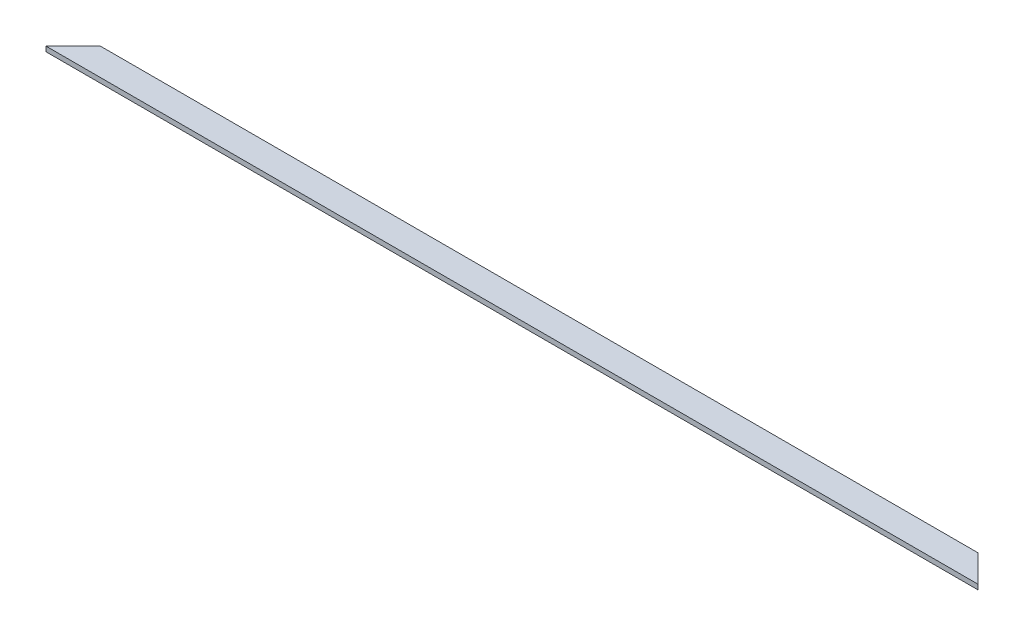
SolidWorks part; units mm, degrees
ref_plane "Front Plane" through (0, 0, 0) normal (0, 0, 1) x (1, 0, 0)
ref_plane "Top Plane" through (0, 0, 0) normal (0, 1, 0) x (1, 0, 0)
ref_plane "Right Plane" through (0, 0, 0) normal (1, 0, 0) x (0, 0, -1)
sketch "Sketch1" plane through (0, 0, 0) normal (0, 1, 0) x (1, 0, 0)
  line L0 (4787.9, 0) -> (4648.2, 139.7)
  line L1 (0, 0) -> (4787.9, 0)
  line L3 (139.7, 139.7) -> (4648.2, 139.7)
  line L4 (0, 0) -> (139.7, 139.7)
  dimension "D1" = 45
  dimension "D2" = 4787.9
  dimension "D3" = 139.7
  dimension "D4" = 45
extrude "Boss-Extrude1" add sketch "Sketch1" along normal blind 25.4
